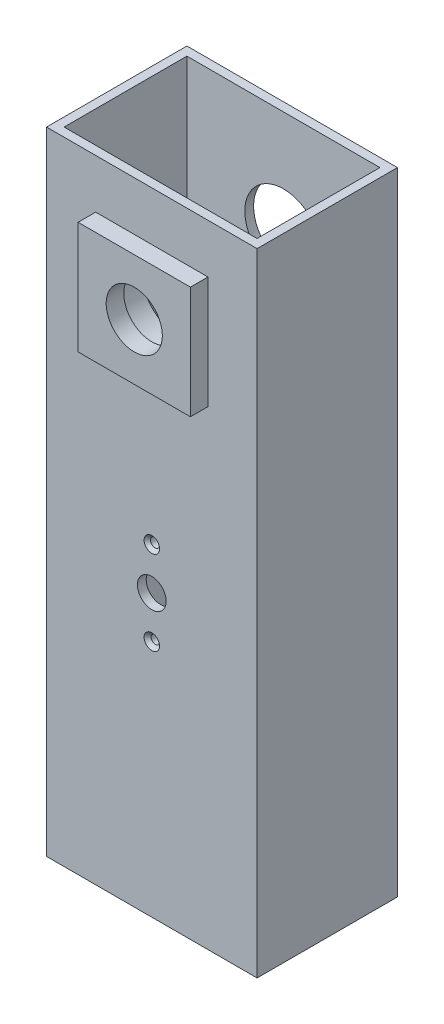
SolidWorks part; units mm, degrees
ref_plane "Front Plane" through (0, 0, 0) normal (0, 0, 1) x (1, 0, 0)
ref_plane "Top Plane" through (0, 0, 0) normal (0, 1, 0) x (1, 0, 0)
ref_plane "Right Plane" through (0, 0, 0) normal (1, 0, 0) x (0, 0, -1)
sketch "Sketch1" plane through (0, 0, 0) normal (0, 1, 0) x (1, 0, 0)
  line L0 (-2.5, -2.5) -> (-57.5, -2.5)
  line L1 (0, 0) -> (-60, 0)
  line L2 (0, 0) -> (0, -40)
  line L3 (0, -40) -> (-60, -40)
  line L4 (-60, 0) -> (-60, -40)
  line L5 (-57.5, -2.5) -> (-57.5, -37.5)
  line L6 (-2.5, -37.5) -> (-57.5, -37.5)
  line L7 (-2.5, -2.5) -> (-2.5, -37.5)
  dimension "D1" = 40
  dimension "D2" = 60
  dimension "D3" = 2.5
extrude "Boss-Extrude1" add sketch "Sketch1" along normal blind 200
sketch "Sketch2" plane through (0, 0, 0) normal (0, 0, -1) x (-1, 0, 0)
  line L0 (60, 200) -> (60, 0) construction
  line L1 (0, 200) -> (60, 200)
  line L2 (0, 200) -> (0, 140)
  line L3 (0, 140) -> (60, 140)
  line L4 (60, 200) -> (60, 140)
  line L5 (0, 200) -> (60, 140)
  circle A0 centre (30, 170) radius 11
  dimension "D2" = 22
  dimension "D1" = 60
extrude "Cut-Extrude1" cut sketch "Sketch2" against normal blind 74.3766 contours L5 A0 | L5 A0
sketch "Sketch3" plane through (0, 0, 37.5) normal (0, 0, -1) x (-1, 0, 0)
  line L1 (10, 150) -> (50, 150)
  line L2 (10, 150) -> (10, 190)
  line L3 (10, 190) -> (50, 190)
  line L4 (50, 150) -> (50, 190)
  line L5 (10, 150) -> (50, 190) construction
  line L6 (10, 190) -> (50, 150) construction
  circle A0 centre (30, 170) radius 11 construction
  circle A1 centre (30, 170) radius 11
  dimension "D1" = 40
  dimension "D2" = 40
extrude "Boss-Extrude2" add sketch "Sketch3" along normal blind 4.5
sketch "Sketch4" plane through (0, 0, 40) normal (0, 0, 1) x (1, 0, 0)
  line L0 (-30, 170) -> (-30, 100)
  circle A0 centre (-30, 100) radius 4
extrude "Cut-Extrude2" cut sketch "Sketch4" against normal blind 258.5
sketch "Sketch5" plane through (0, 0, 0) normal (0, 0, -1) x (-1, 0, 0)
  line L0 (30, 170) -> (30, 20)
  line L1 (30, 20) -> (60, 20)
  line L2 (60, 200) -> (60, 0) construction
  line L3 (60, 20) -> (0, 20)
  line L4 (0, 200) -> (0, 0) construction
  line L6 (0, 20) -> (60, 20)
  line L7 (0, 20) -> (0, 0)
  line L8 (0, 0) -> (60, 0)
  line L9 (60, 20) -> (60, 0)
  line M3 (0, 0) -> (60, 0)
  line M4 (60, 0) -> (60, 200)
  line M6 (0, 200) -> (0, 0)
extrude "Cut-Extrude3" cut sketch "Sketch5" against normal blind 73 contours L1 L3 M6 M3 M4
sketch "Sketch6" plane through (0, 0, 0) normal (0, 0, -1) x (-1, 0, 0)
  circle A0 centre (30, 100) radius 22
  dimension "D1" = 44
extrude "Cut-Extrude4" cut sketch "Sketch6" against normal blind 6
sketch "Sketch7" plane through (0, 0, 40) normal (0, 0, 1) x (1, 0, 0)
  line L0 (-30, 100) -> (-42, 100)
  line L1 (-30, 100) -> (-18, 100)
  circle A0 centre (-42, 100) radius 1
  circle A1 centre (-18, 100) radius 1
extrude "Cut-Extrude5" cut sketch "Sketch7" against normal blind 6
hole_wizard "CSK for M2 Flat Head Machine Screw1" positions "Sketch10" profile "Sketch9" countersink size "M2" standard "ANSI Metric"
sketch "Sketch10" plane through (0, 0, 40) normal (0, 0, 1) x (1, 0, 0)
  point P0 (-42, 100)
  point P3 (-18, 100)
sketch "Sketch9" plane through (-42, 100, 40) normal (1, 0, 0) x (0, -1, 0)
  line L0 (0, 0) -> (0, 15.7811)
  line L1 (0, 15.7811) -> (1.3, 15)
  line L2 (1.3, 15) -> (1.3, 0.9)
  line L3 (1.3, 0.9) -> (2.2, 0)
  line L5 (2.2, 0) -> (0, 0)
  line L6 (-1.3, 0.9) -> (-2.2, 0) construction
  line L10 (0, 15.7811) -> (-1.3, 15) construction
  line L11 (0, -6.35) -> (0, 107.95) construction
  dimension "Hole Dia." = 2.6
  dimension "Hole Depth" = 15
  dimension "Near C'Sink Dia." = 4.4
  dimension "Near C'Sink Angle" = 90
  dimension "Drill Angle" = 118
sketch "Sketch11" plane through (0, 0, 40) normal (0, 0, 1) x (1, 0, 0)
  circle A0 centre (-30, 100) radius 4.1
extrude "Cut-Extrude6" cut sketch "Sketch11" against normal blind 6
sketch "Sketch12" plane through (0, 0, 40) normal (0, 0, 1) x (1, 0, 0)
  line L0 (-30, 100) -> (-30, 88)
  line L1 (-30, 100) -> (-30, 112)
  circle A0 centre (-30, 112) radius 1.2899
  circle A1 centre (-30, 88) radius 0.808
extrude "Cut-Extrude7" cut sketch "Sketch12" against normal blind 6
hole_wizard "CSK for M2 Flat Head Machine Screw3" positions "Sketch15" profile "Sketch16" countersink size "M2" standard "ANSI Metric"
sketch "Sketch15" plane through (0, 0, 40) normal (0, 0, 1) x (1, 0, 0)
  point P0 (-30, 112)
  point P3 (-30, 88)
sketch "Sketch16" plane through (-30, 112, 40) normal (1, 0, 0) x (0, -1, 0)
  line L0 (0, 0) -> (0, 15.721)
  line L1 (0, 15.721) -> (1.2, 15)
  line L2 (1.2, 15) -> (1.2, 1)
  line L3 (1.2, 1) -> (2.2, 0)
  line L5 (2.2, 0) -> (0, 0)
  line L6 (-1.2, 1) -> (-2.2, 0) construction
  line L10 (0, 15.721) -> (-1.2, 15) construction
  line L11 (0, -6.35) -> (0, 107.95) construction
  dimension "Hole Dia." = 2.4
  dimension "Hole Depth" = 15
  dimension "Near C'Sink Dia." = 4.4
  dimension "Near C'Sink Angle" = 90
  dimension "Drill Angle" = 118
sketch "Sketch17" plane through (0, 0, 40) normal (0, 0, 1) x (1, 0, 0)
  line L1 (-15.016, 95.3399) -> (-21.309, 95.3399)
  line L2 (-15.016, 95.3399) -> (-15.016, 104.1228)
  line L3 (-15.016, 104.1228) -> (-21.309, 104.1228)
  line L4 (-21.309, 95.3399) -> (-21.309, 104.1228)
  line L5 (-37.0466, 95.6963) -> (-45.6351, 95.6963)
  line L6 (-37.0466, 95.6963) -> (-37.0466, 105.9046)
  line L7 (-37.0466, 105.9046) -> (-45.6351, 105.9046)
  line L8 (-45.6351, 95.6963) -> (-45.6351, 105.9046)
extrude "Boss-Extrude3" add sketch "Sketch17" against normal blind 2.5
sketch "Sketch18" plane through (0, 0, 33) normal (0, 0, -1) x (-1, 0, 0)
  line L4 (50, 150) -> (50, 190)
  line L5 (50, 190) -> (10, 190)
  line L6 (10, 190) -> (10, 150)
  line L7 (10, 150) -> (50, 150)
  line L8 (50, 150) -> (50, 190)
  line L9 (50, 190) -> (10, 190)
  line L10 (10, 190) -> (10, 150)
  line L11 (10, 150) -> (50, 150)
  circle A0 centre (30, 170) radius 11 construction
  circle A1 centre (30, 170) radius 11
  dimension "D1" = 0
extrude "Boss-Extrude4" add sketch "Sketch18" along normal blind 1
sketch "Sketch19" plane through (0, 0, 40) normal (0, 0, 1) x (1, 0, 0)
  line L1 (-14, 154) -> (-46, 154)
  line L2 (-14, 154) -> (-14, 186)
  line L3 (-14, 186) -> (-46, 186)
  line L4 (-46, 154) -> (-46, 186)
  line L5 (-14, 154) -> (-46, 186) construction
  line L6 (-14, 186) -> (-46, 154) construction
  circle A0 centre (-30, 170) radius 11 construction
  circle A1 centre (-30, 170) radius 11
  point P0 (-30, 170)
  dimension "D1" = 32
  dimension "D2" = 32
extrude "Boss-Extrude5" add sketch "Sketch19" along normal blind 5
sketch "Sketch20" plane through (0, 0, 45) normal (0, 0, 1) x (1, 0, 0)
  circle A0 centre (-30, 170) radius 8
  circle A1 centre (-30, 170) radius 11 construction
  circle A2 centre (-30, 170) radius 11
extrude "Boss-Extrude6" add sketch "Sketch20" against normal blind 5
